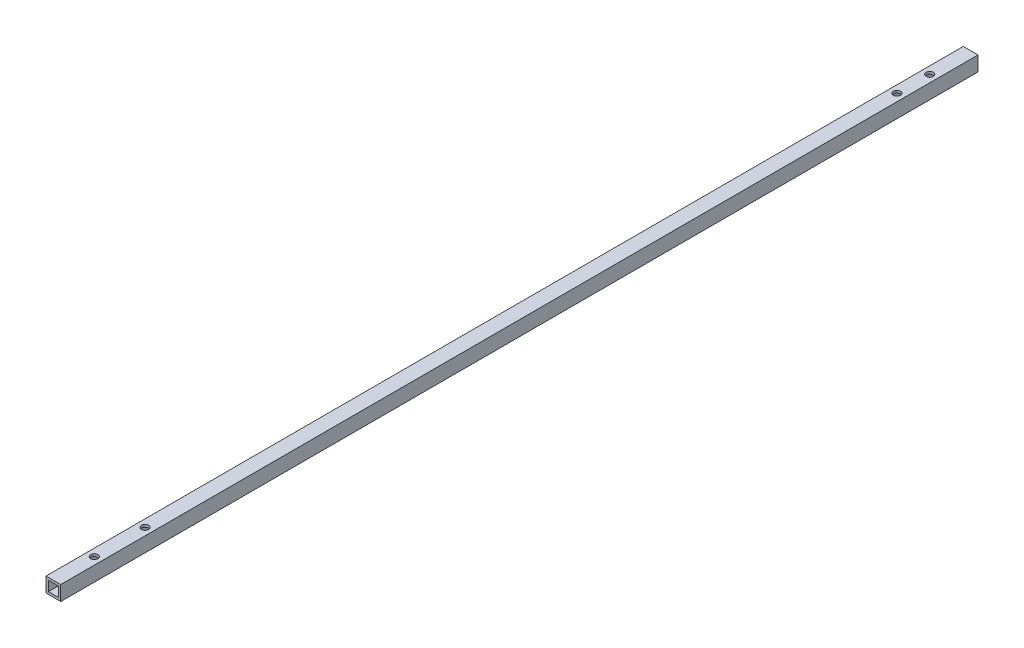
SolidWorks part; units mm, degrees
ref_plane "正面" through (0, 0, 0) normal (0, 0, 1) x (1, 0, 0)
ref_plane "平面" through (0, 0, 0) normal (0, 1, 0) x (1, 0, 0)
ref_plane "右側面" through (0, 0, 0) normal (1, 0, 0) x (0, 0, -1)
sketch "ｽｹｯﾁ1" plane through (0, 0, 0) normal (0, 0, 1) x (1, 0, 0)
  line L1 (-4.5, 4.5) -> (4.5, 4.5)
  line L2 (-4.5, 4.5) -> (-4.5, -4.5)
  line L3 (-4.5, -4.5) -> (4.5, -4.5)
  line L4 (4.5, 4.5) -> (4.5, -4.5)
  line L5 (-4.5, 4.5) -> (4.5, -4.5) construction
  line L6 (-4.5, -4.5) -> (4.5, 4.5) construction
  point P0 (0, 0)
  dimension "D1" = 9
  dimension "D2" = 9
extrude "ﾎﾞｽ - 押し出し1" add sketch "ｽｹｯﾁ1" along normal blind 560.3
sketch "ｽｹｯﾁ2" plane through (0, 0, 560.3) normal (0, 0, 1) x (1, 0, 0)
  line L1 (-3, 3) -> (3, 3)
  line L2 (-3, 3) -> (-3, -3)
  line L3 (-3, -3) -> (3, -3)
  line L4 (3, 3) -> (3, -3)
  line L5 (-3, 3) -> (3, -3) construction
  line L6 (-3, -3) -> (3, 3) construction
  point P0 (0, 0)
  dimension "D1" = 6
  dimension "D2" = 6
extrude "ｶｯﾄ - 押し出し1" cut sketch "ｽｹｯﾁ2" against normal blind 560.3
sketch "ｽｹｯﾁ3" plane through (0, 4.5, 0) normal (0, 1, 0) x (1, 0, 0)
  line L0 (4.5, 0) -> (0, 0)
  line L1 (4.5, 0) -> (-4.5, 0) construction
  line L2 (0, 0) -> (0, -25)
  line L3 (0, 0) -> (4.5, 0)
  line L4 (0, -25) -> (0, -45)
  circle A0 centre (0, -25) radius 2.2
  circle A1 centre (0, -45) radius 2.2
  dimension "D3" = 4.4
  dimension "D4" = 4.4
  dimension "D1" = 25
  dimension "D2" = 20
  dimension "D5" = 4.5
extrude "ｶｯﾄ - 押し出し2" cut sketch "ｽｹｯﾁ3" against normal blind 582
sketch "ｽｹｯﾁ4" plane through (0, 4.5, 0) normal (0, 1, 0) x (1, 0, 0)
  line L0 (4.5, -560.3) -> (0, -560.3)
  line L2 (4.5, -560.3) -> (-4.5, -560.3) construction
  line L3 (0, -560.3) -> (0, -535.3)
  line L4 (0, -535.3) -> (0, -504.3)
  circle A0 centre (0, -535.3) radius 2.2
  circle A1 centre (0, -504.3) radius 2.2
  dimension "D3" = 4.4
  dimension "D4" = 4.4
  dimension "D1" = 4.5
  dimension "D2" = 31
  dimension "D5" = 25
extrude "ｶｯﾄ - 押し出し3" cut sketch "ｽｹｯﾁ4" against normal blind 20
